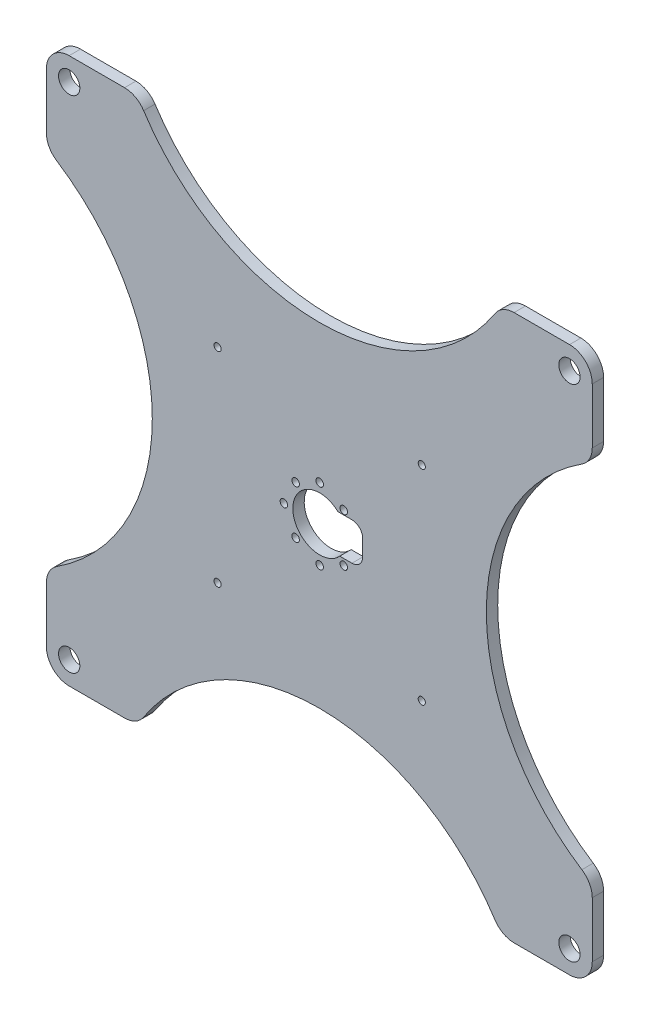
SolidWorks part; units mm, degrees
ref_plane "Front Plane" through (0, 0, 0) normal (0, 0, 1) x (1, 0, 0)
ref_plane "Top Plane" through (0, 0, 0) normal (0, 1, 0) x (1, 0, 0)
ref_plane "Right Plane" through (0, 0, 0) normal (1, 0, 0) x (0, 0, -1)
sketch "Sketch3" plane through (0, 0, 0) normal (0, 0, 1) x (1, 0, 0)
  line L1 (-76.2, -76.2) -> (76.2, -76.2)
  line L2 (-76.2, -76.2) -> (-76.2, 76.2)
  line L3 (-76.2, 76.2) -> (76.2, 76.2)
  line L4 (76.2, -76.2) -> (76.2, 76.2)
  line L5 (-76.2, -76.2) -> (76.2, 76.2) construction
  line L6 (-76.2, 76.2) -> (76.2, -76.2) construction
  point P0 (0, 0)
  dimension "D1" = 152.4
extrude "Boss-Extrude3" add sketch "Sketch3" along normal blind 3.175
sketch "Sketch13" plane through (0.1069, -2.0309, 3.175) normal (0, 0, 1) x (1, 0, 0)
  circle A0 centre (0, 0) radius 7.5
  dimension "D1" = 15
extrude "Cut-Extrude5" cut sketch "Sketch13" against normal through all
sketch "Sketch15" plane through (0.1069, -2.0309, 3.175) normal (0, 0, 1) x (1, 0, 0)
  line L0 (0, 0) -> (0, -36.356) construction
  line L2 (-28.5, -28.5) -> (-28.5, -46) construction
  line L3 (0, 0) -> (-39.3376, 0) construction
  circle A0 centre (-28.5, -28.5) radius 1
  circle A1 centre (-28.5, 28.5) radius 1
  circle A2 centre (28.5, -28.5) radius 1
  circle A3 centre (28.5, 28.5) radius 1
  dimension "D1" = 57
  dimension "D3" = 57
  dimension "D4" = 2
  dimension "D2" = 17.5
extrude "Cut-Extrude6" cut sketch "Sketch15" against normal through all
sketch "Sketch17" plane through (0.1069, -2.0309, 3.175) normal (0, 0, 1) x (1, 0, 0)
  line L1 (0, -5) -> (12, -5)
  line L2 (12, -5) -> (12, 5.5)
  line L3 (12, 5.5) -> (0, 5.5)
  line L5 (0, -5) -> (0, 5.5)
  point P3 (0, 0.25)
  dimension "D1" = 10.5
  dimension "D3" = 12
extrude "Cut-Extrude7" cut sketch "Sketch17" against normal through all
fillet "Fillet1" radius 3 2 edges at (12.1069, 3.4691, 1.5875) (12.1069, -7.0309, 1.5875)
sketch "Sketch19" plane through (0.1069, -2.0309, 3.175) normal (0, 0, 1) x (1, 0, 0)
  line L0 (0, 0) -> (0, 23.9217) construction
  line L1 (0, 0) -> (0, -24.7081) construction
  line L2 (0, 0) -> (-16.3847, 0) construction
  line L3 (0, 0) -> (16.7779, 0) construction
  circle A0 centre (6.72, 6.72) radius 1.05
  circle A1 centre (-6.72, 6.72) radius 1.05
  circle A2 centre (-6.72, -6.72) radius 1.05
  circle A3 centre (6.72, -6.72) radius 1.05
  circle A4 centre (0, 10) radius 1.05
  circle A5 centre (-10, 0) radius 1.05
  circle A6 centre (0, -10) radius 1.05
  dimension "D9" = 2.1
  dimension "D1" = 6.72
  dimension "D2" = 6.72
  dimension "D3" = 6.72
  dimension "D4" = 6.72
  dimension "D5" = 6.72
  dimension "D6" = 6.72
  dimension "D7" = 6.72
  dimension "D8" = 6.72
  dimension "D10" = 10
  dimension "D11" = 10
  dimension "D12" = 10
extrude "Cut-Extrude8" cut sketch "Sketch19" against normal through all
sketch "Sketch20" plane through (0, 0, 3.175) normal (0, 0, 1) x (1, 0, 0)
  line L1 (-69.83, -69.83) -> (69.83, -69.83) construction
  line L2 (-69.83, -69.83) -> (-69.83, 69.83) construction
  line L3 (-69.83, 69.83) -> (69.83, 69.83) construction
  line L4 (69.83, -69.83) -> (69.83, 69.83) construction
  line L5 (-69.83, -69.83) -> (69.83, 69.83) construction
  line L6 (-69.83, 69.83) -> (69.83, -69.83) construction
  circle A0 centre (-69.83, 69.83) radius 2.9718
  circle A1 centre (69.83, 69.83) radius 2.9718
  circle A2 centre (69.83, -69.83) radius 2.9718
  circle A3 centre (-69.83, -69.83) radius 2.9718
  point P0 (0, 0)
  point P11 (0, 0)
  dimension "D1" = 4
  dimension "D2" = 139.66
  dimension "D3" = 5.9436
extrude "Bolt Holes" cut sketch "Sketch20" against normal through all both and the other way through all
sketch "Sketch21" plane through (0, 0, 3.175) normal (0, 0, 1) x (1, 0, 0)
  line L1 (-39.6561, -36.877) -> (39.6561, -36.877)
  line L2 (-39.6561, -36.877) -> (-39.6561, 36.877)
  line L3 (-39.6561, 36.877) -> (39.6561, 36.877)
  line L4 (39.6561, -36.877) -> (39.6561, 36.877)
  line L5 (-39.6561, -36.877) -> (39.6561, 36.877) construction
  line L6 (-39.6561, 36.877) -> (39.6561, -36.877) construction
  point P0 (0, 0)
ref_plane "Mirror" through (0, 0, 0) normal (0.7071, -0.7071, 0) x (-0.7071, -0.7071, 0)
sketch "Sketch25" plane through (0, 0, 3.175) normal (0, 0, 1) x (1, 0, 0)
  line L0 (-76.2, 76.2) -> (-76.2, -76.2) construction
  line L1 (76.2, 76.2) -> (-76.2, 76.2) construction
  line L2 (-76.2, -76.2) -> (76.2, -76.2) construction
  line L3 (-76.2, 50.8) -> (-76.2, -50.8)
  arc A0 (-76.2, 50.8) -> (-76.2, -50.8) centre (-105.0489, 0) cw
  dimension "D3" = 58.42
  dimension "D1" = 25.4
  dimension "D2" = 25.4
extrude "Cut-Extrude12" cut sketch "Sketch25" against normal up to surface (3.175 mm away) up to face at (-66.8582, -69.83, 0)
fillet "Fillet2" radius 6.35 4 edges at (-76.2, -76.2, 1.5875) (-76.2, -50.8, 1.5875) (-76.2, 50.8, 1.5875) (-76.2, 76.2, 1.5875)
ref_plane "Plane3" through (0, 0, 0) normal (-0.7071, -0.7071, 0) x (-0.7071, 0.7071, 0)
mirror "Mirror4" about plane through (0, 0, 0) normal (0.7071, -0.7071, 0) of "Cut-Extrude12"
mirror "Mirror5" about plane through (0, 0, 0) normal (-0.7071, -0.7071, 0) of "Mirror4", "Cut-Extrude12"
fillet "Fillet3" radius 6.35 6 edges at (76.2, 76.2, 1.5875) (76.2, 50.8, 1.5875) (76.2, -50.8, 1.5875) (76.2, -76.2, 1.5875) (50.8, -76.2, 1.5875) (-50.8, -76.2, 1.5875)
fillet "Fillet4" radius 6.35 2 edges at (-50.8, 76.2, 1.5875) (50.8, 76.2, 1.5875)
